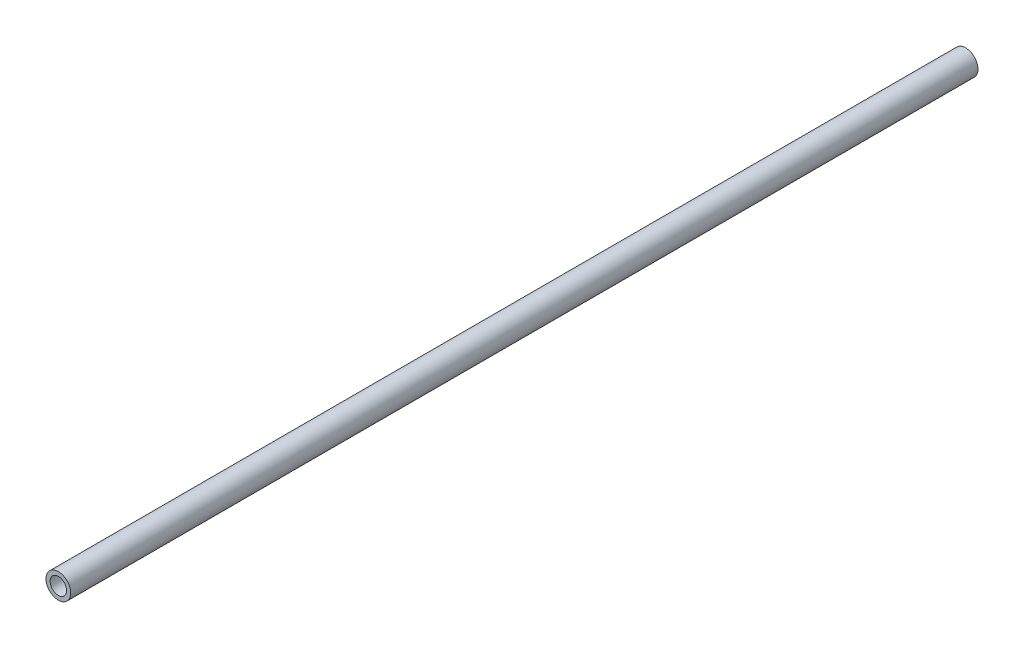
SolidWorks part; units mm, degrees
material "PVC Rigid"
ref_plane "Front Plane" through (0, 0, 0) normal (0, 0, 1) x (1, 0, 0)
ref_plane "Top Plane" through (0, 0, 0) normal (0, 1, 0) x (1, 0, 0)
ref_plane "Right Plane" through (0, 0, 0) normal (1, 0, 0) x (0, 0, -1)
sketch "Sketch1" plane through (0, 0, 0) normal (0, 0, 1) x (1, 0, 0)
  circle A0 centre (0, 0) radius 7.62
  circle A2 centre (0, 0) radius 5.08
  dimension "D1" = 15.24
  dimension "D2" = 10.16
extrude "Boss-Extrude1" add sketch "Sketch1" along normal blind 558.8
